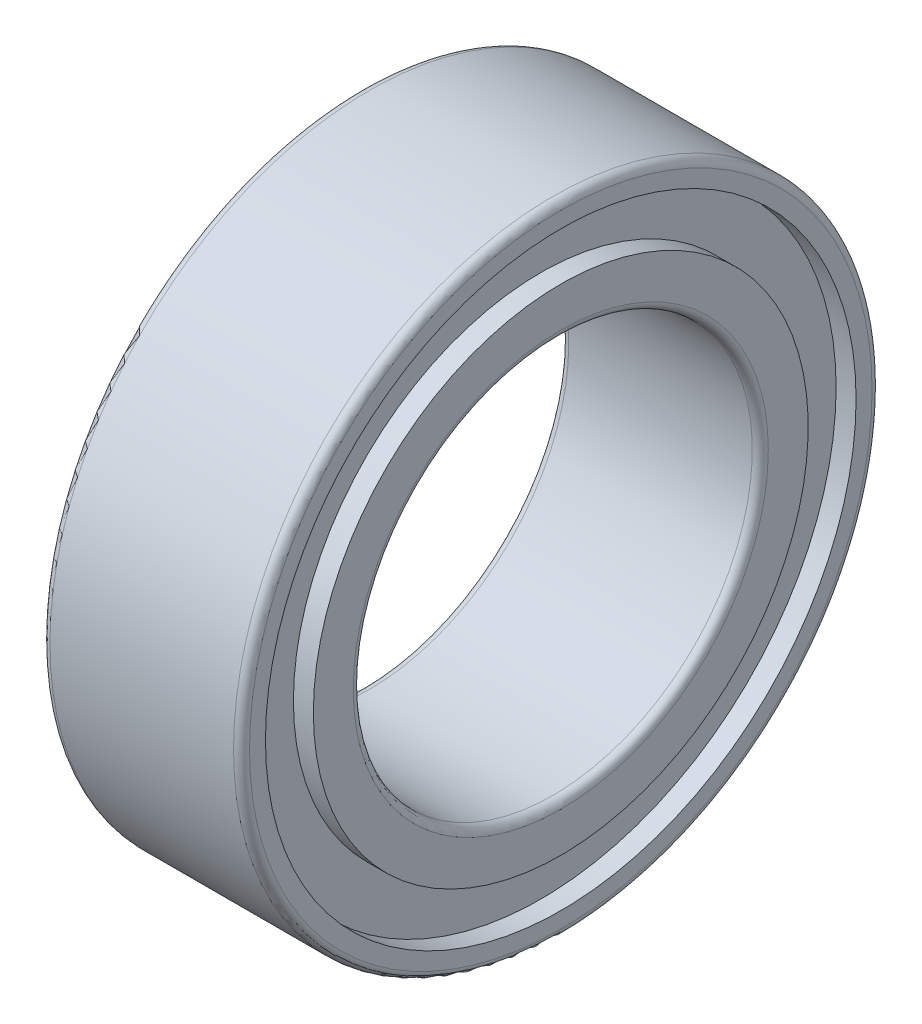
SolidWorks part; units mm, degrees
ref_plane "Front Plane" through (0, 0, 0) normal (0, 0, 1) x (1, 0, 0)
ref_plane "Top Plane" through (0, 0, 0) normal (0, 1, 0) x (1, 0, 0)
ref_plane "Right Plane" through (0, 0, 0) normal (1, 0, 0) x (0, 0, -1)
sketch "Sketch1" plane through (0, 0, 0) normal (0, 0, 1) x (1, 0, 0)
  line L0 (0, 0) -> (2.5, 0) construction
  line L1 (0, 4) -> (0, 3.7)
  line L2 (0, 2.5) -> (2.5, 2.5)
  line L3 (2.5, 2.5) -> (2.5, 3.1)
  line L4 (2.5, 4) -> (0, 4)
  line L5 (0, 3.7) -> (0.25, 3.7)
  line L6 (0.25, 3.7) -> (0.25, 3.1)
  line L7 (0.25, 3.1) -> (0, 3.1)
  line L8 (2.5, 3.7) -> (2.25, 3.7)
  line L9 (2.25, 3.7) -> (2.25, 3.1)
  line L10 (2.25, 3.1) -> (2.5, 3.1)
  line L11 (0, 3.1) -> (0, 2.5)
  line L12 (2.5, 3.7) -> (2.5, 4)
  dimension "B" = 2.5
  dimension "D_s" = 5
  dimension "D" = 8
  dimension "MSM_5" = 2
  dimension "MSM_3" = 6.2
  dimension "MSM_4" = 7.4
revolve "Revolve1" add sketch "Sketch1" angle 360 about L0
fillet "Fillet1" radius 0.1 4 edges at (0, 0, 2.5) (0, 0, 4) (2.5, 0, 2.5) (2.5, 0, 4)
